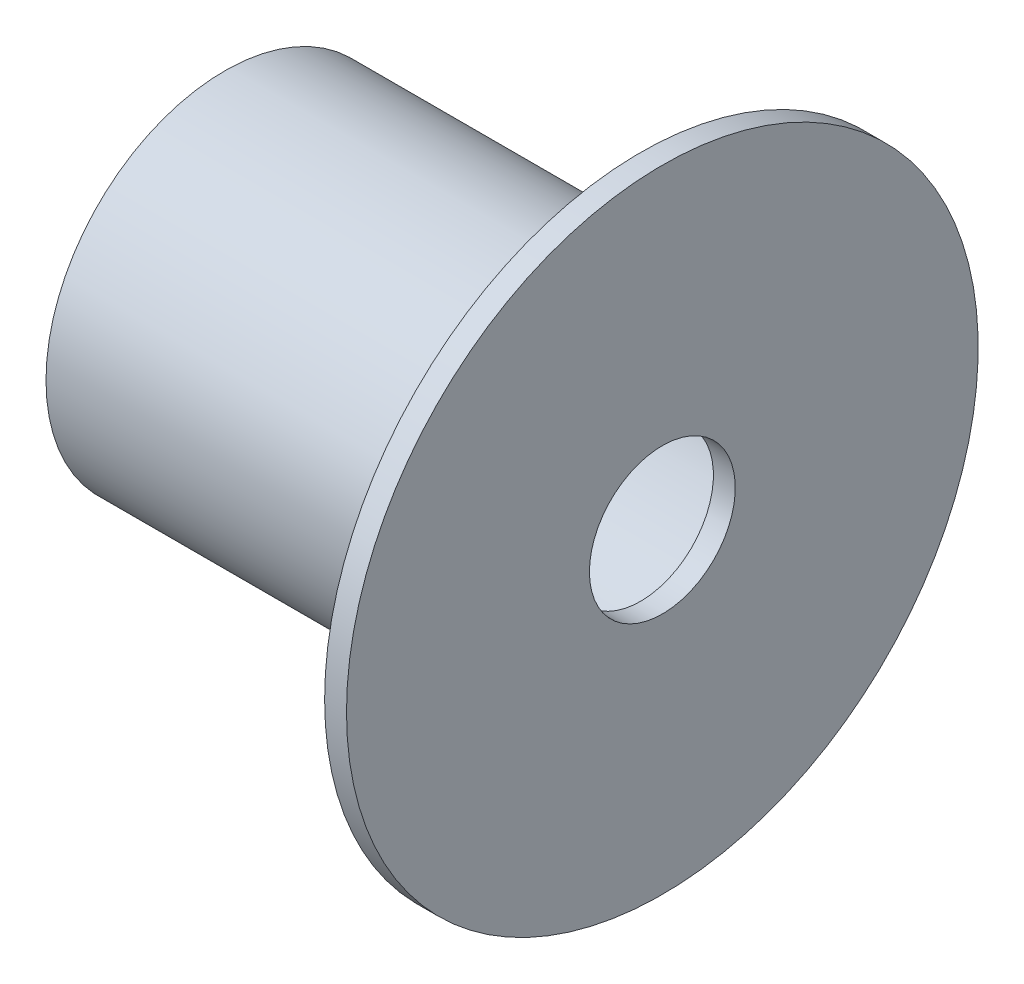
SolidWorks part; units mm, degrees
ref_plane "Front Plane" through (0, 0, 0) normal (0, 0, 1) x (1, 0, 0)
ref_plane "Top Plane" through (0, 0, 0) normal (0, 1, 0) x (1, 0, 0)
ref_plane "Right Plane" through (0, 0, 0) normal (1, 0, 0) x (0, 0, -1)
sketch "Sketch1" plane through (0, 0, 0) normal (0, 0, 1) x (1, 0, 0)
  line L0 (-17.7627, -2.0938) -> (34.2373, -2.0938) construction
  line L1 (-17.7627, -1.5938) -> (-17.7627, -2.5938) construction
  line L2 (34.2373, -4.3438) -> (34.2373, 0.1562) construction
  line L3 (25.4089, -21.0938) -> (25.4089, 16.9062) construction
  line L4 (25.4089, 7.9062) -> (28.4089, 7.9062)
  line L5 (25.4089, 7.9062) -> (25.4089, 20.414)
  line L6 (25.4089, 41.2134) -> (28.4089, 41.2134)
  line L7 (28.4089, 7.9062) -> (28.4089, 41.2134)
  line L8 (25.4089, 22.414) -> (25.4089, 41.2134)
  line L9 (25.4089, 20.414) -> (-31.5911, 20.414)
  line L11 (25.4089, 22.414) -> (-31.5911, 22.414)
  line L12 (-31.5911, 20.414) -> (-31.5911, 22.414)
  dimension "D1" = 3
  dimension "D2" = 2
  dimension "D3" = 10
  dimension "D4" = 57
revolve "Revolve1" add sketch "Sketch1" angle 360 about L0
